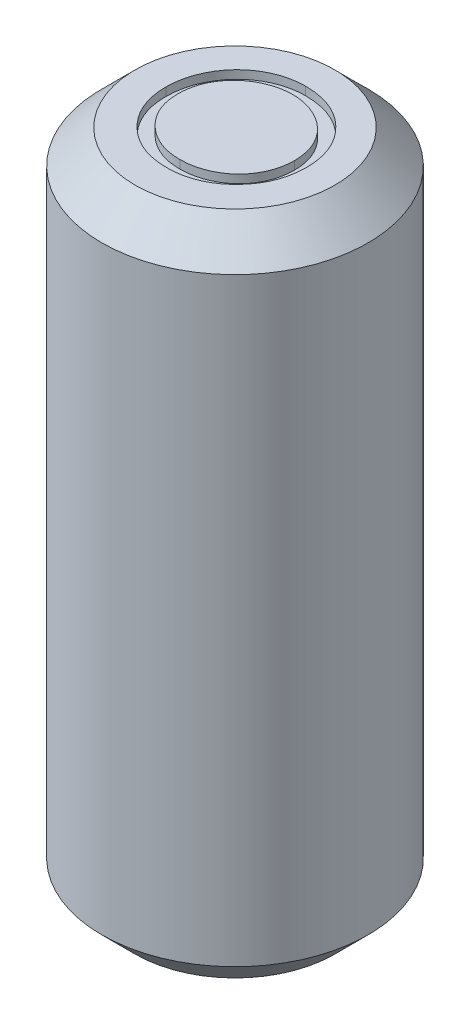
SolidWorks part; units mm, degrees
ref_plane "Alzado" through (0, 0, 0) normal (0, 0, 1) x (1, 0, 0)
ref_plane "Planta" through (0, 0, 0) normal (0, 1, 0) x (1, 0, 0)
ref_plane "Vista lateral" through (0, 0, 0) normal (1, 0, 0) x (0, 0, -1)
sketch "Croquis1" plane through (0, 0, 0) normal (0, 1, 0) x (1, 0, 0)
  circle A0 centre (0, 0) radius 4
  dimension "D1" = 8
extrude "Saliente-Extruir1" add sketch "Croquis1" along normal blind 20
chamfer "Chaflán1" distance 1 angle 45 2 edges at (0, 0, 4) (0, 20, 4)
sketch "Croquis3" plane through (0, 20, 0) normal (0, 1, 0) x (1, 0, 0)
  text T0 "X" font "Century Gothic" height 4
extrude "Cortar-Extruir1" [suppressed] cut sketch "Croquis3" against normal blind 0.25
sketch "Croquis4" plane through (0, 20, 0) normal (0, 1, 0) x (1, 0, 0)
  text T0 "O" font "Century Gothic" height 4
extrude "Cortar-Extruir2" cut sketch "Croquis4" against normal blind 0.25
